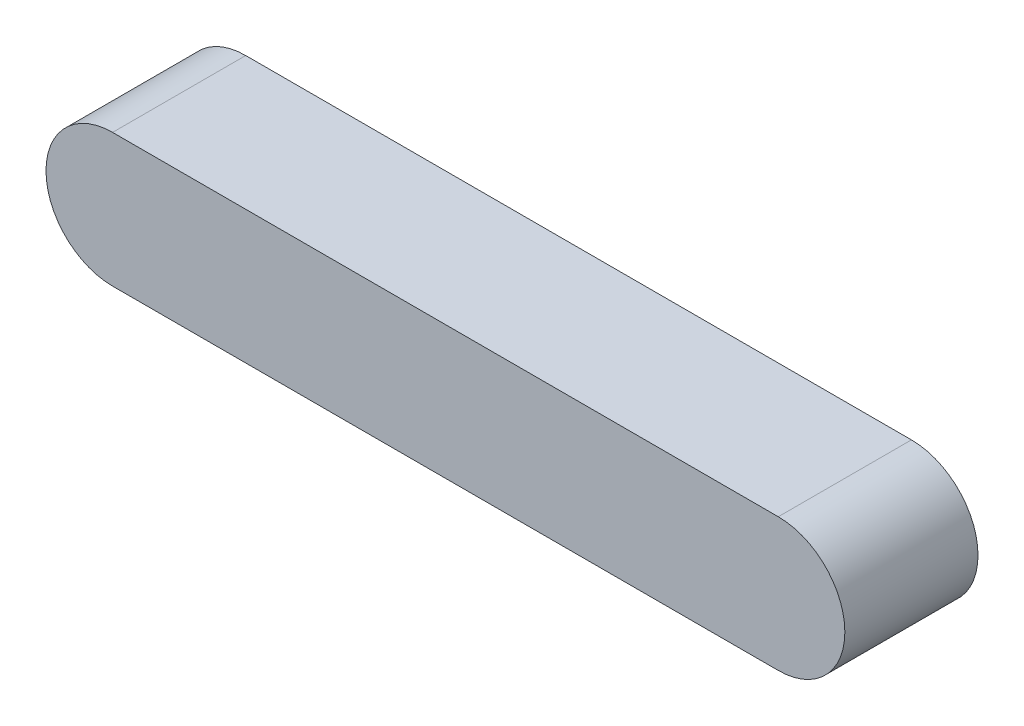
SolidWorks part; units mm, degrees
ref_plane "Front Plane" through (0, 0, 0) normal (0, 0, 1) x (1, 0, 0)
ref_plane "Top Plane" through (0, 0, 0) normal (0, 1, 0) x (1, 0, 0)
ref_plane "Right Plane" through (0, 0, 0) normal (1, 0, 0) x (0, 0, -1)
sketch "Sketch1" plane through (0, 0, 0) normal (0, 0, 1) x (1, 0, 0)
  line L0 (-127, 0) -> (127, 0) construction
  line L1 (-127, 25.4) -> (127, 25.4)
  line L2 (-127, -25.4) -> (127, -25.4)
  arc A0 (-127, 25.4) -> (-127, -25.4) centre (-127, 0) ccw
  arc A1 (127, -25.4) -> (127, 25.4) centre (127, 0) ccw
  point P2 (0, 0)
  dimension "D1" = 254
  dimension "D2" = 50.8
extrude "Boss-Extrude1" add sketch "Sketch1" along normal blind 50.8
